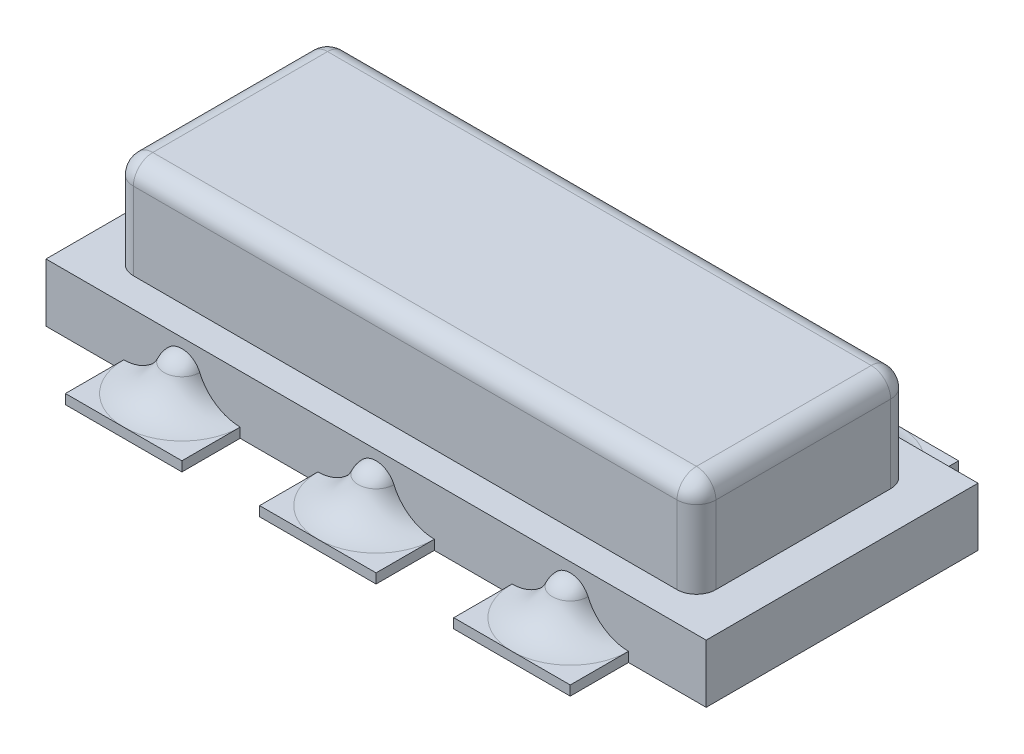
SolidWorks part; units mm, degrees
material "E-Glass Fiber"
ref_plane "Front Plane" through (0, 0, 0) normal (0, 0, 1) x (1, 0, 0)
ref_plane "Top Plane" through (0, 0, 0) normal (0, 1, 0) x (1, 0, 0)
ref_plane "Right Plane" through (0, 0, 0) normal (1, 0, 0) x (0, 0, -1)
sketch "Sketch1" plane through (0, 0, 0) normal (0, 1, 0) x (1, 0, 0)
  line L0 (0, -55) -> (0, 55) construction
  line L1 (-1.7, 0.7) -> (1.7, 0.7)
  line L2 (-1.7, 0.7) -> (-1.7, -0.7)
  line L3 (-1.7, -0.7) -> (1.7, -0.7)
  line L4 (1.7, 0.7) -> (1.7, -0.7)
  line L5 (-55, 0) -> (55, 0) construction
  dimension "D1" = 3.4
  dimension "D2" = 1.4
  dimension "D3" = 1.7
  dimension "D4" = 0.7
extrude "Boss-Extrude1" add sketch "Sketch1" along normal blind 0.3
sketch "Sketch2" plane through (0, 0.3, 0) normal (0, 1, 0) x (1, 0, 0)
  line L0 (-0.165, 0) -> (0.165, 0) construction
  line L1 (-1.4, 0.55) -> (1.4, 0.55)
  line L2 (-1.5, 0.45) -> (-1.5, -0.45)
  line L3 (-1.4, -0.55) -> (1.4, -0.55)
  line L4 (1.5, 0.45) -> (1.5, -0.45)
  line L5 (0, -0.165) -> (0, 0.165) construction
  arc A0 (-1.5, -0.45) -> (-1.4, -0.55) centre (-1.4, -0.45) ccw
  arc A1 (1.4, -0.55) -> (1.5, -0.45) centre (1.4, -0.45) ccw
  arc A2 (1.4, 0.55) -> (1.5, 0.45) centre (1.4, 0.45) cw
  arc A3 (-1.4, 0.55) -> (-1.5, 0.45) centre (-1.4, 0.45) ccw
  dimension "D5" = 0.1
  dimension "D1" = 1.1
  dimension "D2" = 0.55
  dimension "D3" = 3
  dimension "D4" = 1.5
extrude "Boss-Extrude2" add sketch "Sketch2" along normal blind 0.5
fillet "Fillet1" radius 0.1 8 edges at (-1.4707, 0.8, 0.5207) (-1.5, 0.8, 0) (-1.4707, 0.8, -0.5207) (0, 0.8, -0.55) (1.4707, 0.8, -0.5207) (1.5, 0.8, 0) (1.4707, 0.8, 0.5207) (0, 0.8, 0.55)
sketch "Sketch3" plane through (0, 0, 0) normal (0, 1, 0) x (1, 0, 0)
  line L0 (0, -0.44) -> (0, 0.44) construction
  line L1 (-1.3, 1) -> (-0.7, 1)
  line L2 (-1.3, 1) -> (-1.3, -1)
  line L3 (-1.3, -1) -> (-0.7, -1)
  line L4 (-0.7, 1) -> (-0.7, -1)
  line L5 (-0.3, 1) -> (0.3, 1)
  line L6 (-0.3, 1) -> (-0.3, -1)
  line L7 (-0.3, -1) -> (0.3, -1)
  line L8 (0.3, 1) -> (0.3, -1)
  line L9 (0.7, 1) -> (1.3, 1)
  line L10 (0.7, 1) -> (0.7, -1)
  line L11 (0.7, -1) -> (1.3, -1)
  line L12 (1.3, 1) -> (1.3, -1)
  line L13 (-0.44, 0) -> (0.44, 0) construction
  dimension "D1" = 1
  dimension "D2" = 1
  dimension "D3" = 0.3
  dimension "D4" = 0.6
  dimension "D5" = 2
  dimension "D6" = 1
extrude "Boss-Extrude3" add sketch "Sketch3" along normal blind 0.05
ref_plane "Plane1" through (-1, 0, 0) normal (1, 0, 0) x (0, 0, -1)
sketch "Sketch4" plane through (-1, 0, 0) normal (1, 0, 0) x (0, 0, -1)
  line L0 (0.7, 0.3) -> (0.7, -0.2161) construction
  line L1 (0.7, 0.3) -> (0.7, 0) construction
  line L2 (0.7, 0.3) -> (-0.7, 0.3) construction
  line L3 (0.7, 0.25) -> (0.3822, 0.25) construction
  line L5 (1, 0.05) -> (0.7, 0.05) construction
  line L7 (0.7, 0.25) -> (0.7, 0.05)
  line L8 (0.7, 0.05) -> (1, 0.05)
  arc A0 (0.7, 0.25) -> (0.7919, 0.1894) centre (0.7, 0.15) cw
  arc A1 (0.7919, 0.1894) -> (1, 0.05) centre (1.0033, 0.28) ccw
  dimension "D2" = 0.1
  dimension "D4" = 0.23
  dimension "D1" = 0.6
  dimension "D3" = 0.2
revolve "Revolve2" add sketch "Sketch4" angle 360 about L0
pattern_linear "LPattern1" count 3 spacing 1 along (1, 0, 0) count 2 spacing 1.4 along (0, 0, 1) of "Revolve2"
